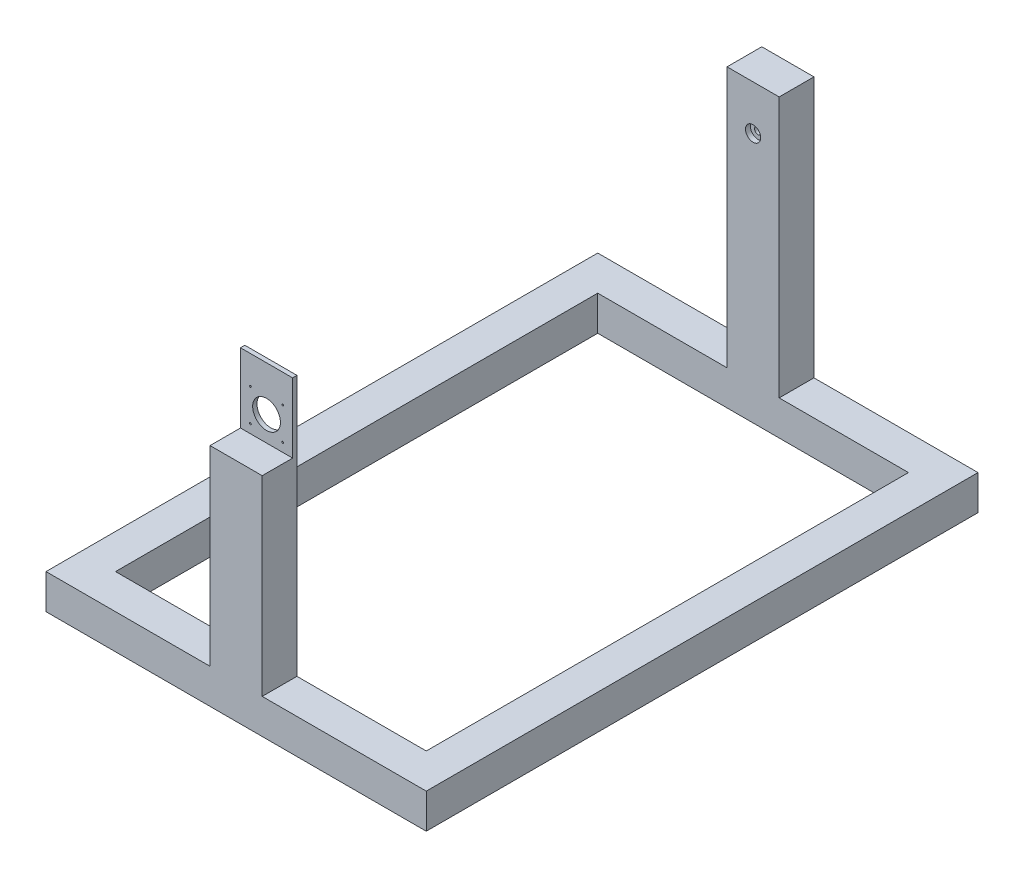
SolidWorks part; units mm, degrees
ref_plane "Front Plane" through (0, 0, 0) normal (0, 0, 1) x (1, 0, 0)
ref_plane "Top Plane" through (0, 0, 0) normal (0, 1, 0) x (1, 0, 0)
ref_plane "Right Plane" through (0, 0, 0) normal (1, 0, 0) x (0, 0, -1)
sketch "Sketch1" plane through (0, 0, 0) normal (0, 1, 0) x (1, 0, 0)
  line L0 (0, -55) -> (0, 55) construction
  line L1 (-277.9, 25.4) -> (277.9, 25.4)
  line L2 (-277.9, 25.4) -> (-277.9, -25.4)
  line L3 (-227.1, -25.4) -> (227.1, -25.4)
  line L4 (277.9, 25.4) -> (277.9, -25.4)
  line L5 (-55, 0) -> (55, 0) construction
  line L8 (-277.9, -25.4) -> (-277.9, -781.0482)
  line L9 (-277.9, -781.0482) -> (-227.1, -781.0482)
  line L10 (-227.1, -25.4) -> (-227.1, -730.2482)
  line L12 (277.9, -25.4) -> (277.9, -781.0482)
  line L13 (277.9, -781.0482) -> (227.1, -781.0482)
  line L14 (227.1, -25.4) -> (227.1, -730.2482)
  line L15 (227.1, -781.0482) -> (-227.1, -781.0482)
  line L17 (227.1, -730.2482) -> (-227.1, -730.2482)
  dimension "D1" = 555.8
  dimension "D2" = 277.9
  dimension "D3" = 50.8
  dimension "D4" = 25.4
  dimension "D5" = 50.8
  dimension "D7" = 755.6482
  dimension "D8" = 50.8
  dimension "D9" = 50.8
extrude "Boss-Extrude1" add sketch "Sketch1" along normal blind 50.8
sketch "Sketch2" plane through (0, 50.8, 0) normal (0, 1, 0) x (1, 0, 0)
  line L0 (-227.1, -730.2482) -> (227.1, -730.2482) construction
  line L1 (-38.1, -730.2482) -> (38.1, -730.2482)
  line L2 (-38.1, -730.2482) -> (-38.1, -781.0482)
  line L3 (-38.1, -781.0482) -> (38.1, -781.0482)
  line L4 (38.1, -730.2482) -> (38.1, -781.0482)
  line L5 (-277.9, -781.0482) -> (277.9, -781.0482) construction
  line L6 (-277.9, 25.4) -> (-277.9, -781.0482) construction
  dimension "D1" = 76.2
  dimension "D2" = 239.8
extrude "Boss-Extrude2" add sketch "Sketch2" along normal blind 279.4
sketch "Sketch4" plane through (0, 50.8, 0) normal (0, 1, 0) x (1, 0, 0)
  line L0 (277.9, 25.4) -> (-277.9, 25.4) construction
  line L1 (-38.1, 25.4) -> (38.1, 25.4)
  line L2 (-38.1, 25.4) -> (-38.1, -25.4)
  line L3 (-38.1, -25.4) -> (38.1, -25.4)
  line L4 (38.1, 25.4) -> (38.1, -25.4)
  line L5 (227.1, -25.4) -> (-227.1, -25.4) construction
  line L6 (-277.9, 25.4) -> (-277.9, -781.0482) construction
  dimension "D1" = 76.2
  dimension "D2" = 239.8
extrude "Boss-Extrude3" add sketch "Sketch4" along normal blind 381
sketch "Sketch5" plane through (0, 330.2, 0) normal (0, 1, 0) x (1, 0, 0)
  line L0 (38.1, -781.0482) -> (38.1, -730.2482) construction
  line L1 (-38.1, -730.2482) -> (38.1, -730.2482)
  line L2 (-38.1, -730.2482) -> (-38.1, -736.5982)
  line L3 (-38.1, -736.5982) -> (38.1, -736.5982)
  line L4 (38.1, -730.2482) -> (38.1, -736.5982)
  dimension "D1" = 6.35
extrude "Boss-Extrude4" add sketch "Sketch5" along normal blind 101.6
sketch "Sketch6" plane through (0, 0, 736.5982) normal (0, 0, 1) x (1, 0, 0)
  line L0 (38.1, 431.8) -> (38.1, 330.2) construction
  line L2 (-38.1, 431.8) -> (-38.1, 330.2) construction
  line L3 (-38.1, 330.2) -> (38.1, 330.2) construction
  line L4 (-38.1, 431.8) -> (38.1, 431.8) construction
  circle A1 centre (-23.5732, 390.0463) radius 1.27
  circle A2 centre (-23.5732, 342.9) radius 1.27
  circle A3 centre (23.5732, 390.0463) radius 1.27
  circle A4 centre (23.5732, 342.9) radius 1.27
  circle A5 centre (0, 366.4732) radius 20.32
  dimension "D4" = 2.54
  dimension "D5" = 2.54
  dimension "D9" = 2.54
  dimension "D11" = 2.54
  dimension "D2" = 40.64
  dimension "D3" = 14.5268
  dimension "D6" = 14.5268
  dimension "D7" = 12.7
  dimension "D8" = 47.1463
  dimension "D10" = 12.7
  dimension "D12" = 47.1463
  dimension "D13" = 14.5268
  dimension "D14" = 14.5268
  dimension "D15" = 47.1463
  dimension "D16" = 65.3268
  dimension "D17" = 38.1
extrude "Cut-Extrude2" cut sketch "Sketch6" against normal blind 6.35
sketch "Sketch8" plane through (0, 0, 25.4) normal (0, 0, 1) x (1, 0, 0)
  line L0 (38.1, 431.8) -> (38.1, 50.8) construction
  line L1 (-38.1, 431.8) -> (38.1, 431.8) construction
  circle A0 centre (0, 366.4732) radius 11.1125
  dimension "D3" = 22.225
  dimension "D1" = 38.1
  dimension "D2" = 65.3268
extrude "Cut-Extrude4" cut sketch "Sketch8" against normal blind 7.1437
sketch "Sketch9" plane through (0, 0, 18.2563) normal (0, 0, 1) x (1, 0, 0)
  circle A0 centre (0, 366.4732) radius 5.08
  point P3 (0, 0)
  dimension "D1" = 10.16
extrude "Cut-Extrude5" cut sketch "Sketch9" against normal blind 50.8
